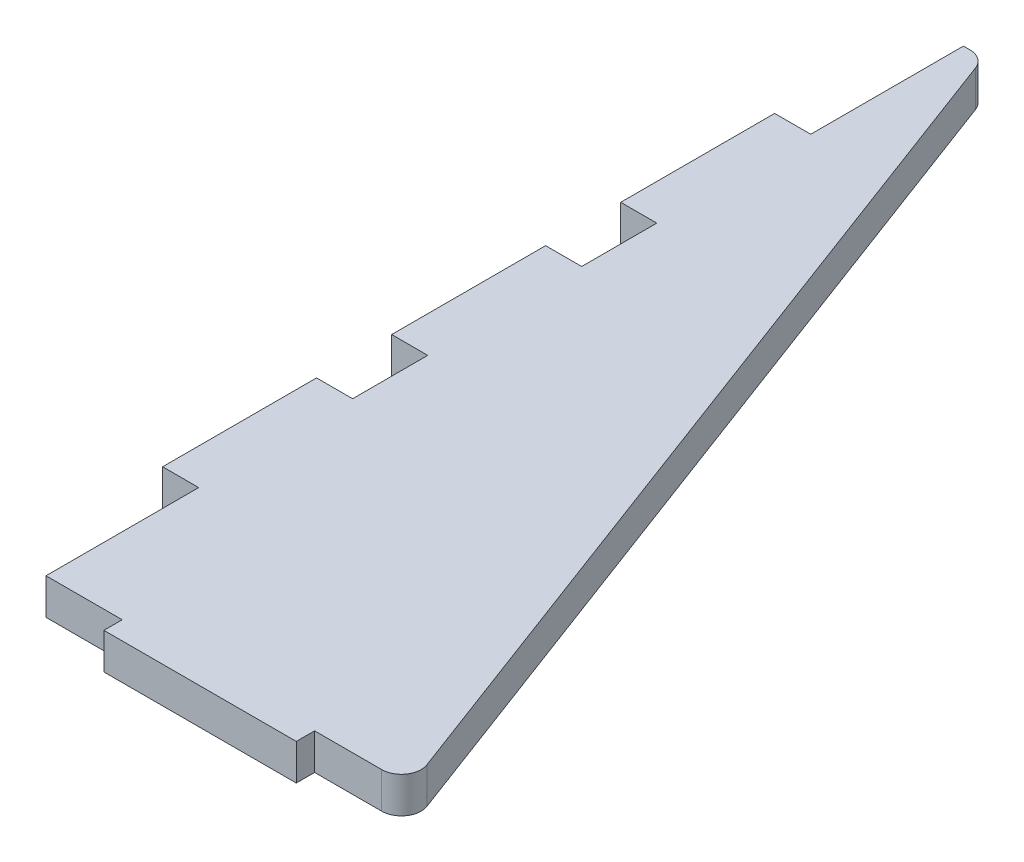
SolidWorks part; units mm, degrees
material "Balsa"
ref_plane "Front Plane" through (0, 0, 0) normal (0, 0, 1) x (1, 0, 0)
ref_plane "Top Plane" through (0, 0, 0) normal (0, 1, 0) x (1, 0, 0)
ref_plane "Right Plane" through (0, 0, 0) normal (1, 0, 0) x (0, 0, -1)
sketch "Sketch1" plane through (0, 0, 0) normal (0, 1, 0) x (1, 0, 0)
  line L0 (-3.175, 76.2) -> (-3.175, -76.2)
  line L1 (-3.175, -76.2) -> (57.15, -76.2)
  line L2 (57.15, -76.2) -> (0, 76.2)
  line L3 (0, 76.2) -> (-3.175, 76.2)
  point P2 (0, 0)
  point P5 (0, 0)
  point P7 (28.575, 0)
  dimension "D1" = 152.4
  dimension "D2" = 3.175
  dimension "D3" = 57.15
extrude "Boss-Extrude1" add sketch "Sketch1" along normal blind 6 contours L2 L3 L0 L1
sketch "Sketch2" plane through (0, 0, 0) normal (0, 1, 0) x (1, 0, 0)
  line L0 (-3.175, 76.2) -> (-3.175, -76.2) construction
  line L1 (-3.175, -12.7) -> (-9.175, -12.7)
  line L2 (-3.175, -12.7) -> (-3.175, 12.7)
  line L3 (-3.175, 12.7) -> (-9.175, 12.7)
  line L4 (-9.175, -12.7) -> (-9.175, 12.7)
  line L5 (-25.5719, 0) -> (49.4388, 0) construction
  line L6 (-3.175, 25.4) -> (-9.175, 25.4)
  line L7 (-3.175, 25.4) -> (-3.175, 50.8)
  line L8 (-3.175, 50.8) -> (-9.175, 50.8)
  line L9 (-9.175, 25.4) -> (-9.175, 50.8)
  line L10 (-3.175, -25.4) -> (-3.175, -50.8)
  line L11 (-3.175, -25.4) -> (-9.175, -25.4)
  line L12 (-9.175, -25.4) -> (-9.175, -50.8)
  line L13 (-3.175, -50.8) -> (-9.175, -50.8)
  line L14 (-3.175, -76.2) -> (57.15, -76.2) construction
  line L15 (9.4996, -76.2) -> (41.3004, -76.2)
  line L16 (9.4996, -76.2) -> (9.4996, -79.248)
  line L17 (9.4996, -79.248) -> (41.3004, -79.248)
  line L18 (41.3004, -76.2) -> (41.3004, -79.248)
  point P13 (-9.175, 0)
  point P14 (-9.175, 38.1)
  point P25 (25.4, -79.248)
  dimension "D1" = 6
  dimension "D2" = 25.4
  dimension "D3" = 38.1
  dimension "D4" = 25.4
  dimension "D5" = 31.8008
  dimension "D6" = 3.048
extrude "Boss-Extrude4" add sketch "Sketch2" along normal up to surface (6 mm away) up to face at (12.7, 6, 0)
fillet "Fillet1" radius 3.175 2 edges at (57.15, 3, 76.2) (0, 3, -76.2)
sketch "Sketch3" plane through (0, 6, 0) normal (0, 1, 0) x (1, 0, 0)
  line L40 (41.402, -76.3016) -> (52.5685, -76.3016)
  line L41 (55.6364, -71.8745) -> (0.8677, 74.1755)
  line L42 (-2.2003, 76.3016) -> (-3.2766, 76.3016)
  line L43 (-3.2766, 76.3016) -> (-3.2766, 50.9016)
  line L44 (-3.2766, 50.9016) -> (-9.2766, 50.9016)
  line L45 (-9.2766, 50.9016) -> (-9.2766, 25.2984)
  line L46 (-9.2766, 25.2984) -> (-3.2766, 25.2984)
  line L47 (-3.2766, 25.2984) -> (-3.2766, 12.8016)
  line L48 (-3.2766, 12.8016) -> (-9.2766, 12.8016)
  line L49 (-9.2766, 12.8016) -> (-9.2766, -12.8016)
  line L50 (-9.2766, -12.8016) -> (-3.2766, -12.8016)
  line L51 (-3.2766, -12.8016) -> (-3.2766, -25.2984)
  line L52 (-3.2766, -25.2984) -> (-9.2766, -25.2984)
  line L53 (-9.2766, -25.2984) -> (-9.2766, -50.9016)
  line L54 (-9.2766, -50.9016) -> (-3.2766, -50.9016)
  line L55 (-3.2766, -50.9016) -> (-3.2766, -76.3016)
  line L56 (-3.2766, -76.3016) -> (9.398, -76.3016)
  line L57 (9.398, -76.3016) -> (9.398, -79.3496)
  line L58 (9.398, -79.3496) -> (41.402, -79.3496)
  line L59 (41.402, -79.3496) -> (41.402, -76.3016)
  line L60 (41.402, -76.3016) -> (52.5685, -76.3016)
  line L61 (55.6364, -71.8745) -> (0.8677, 74.1755)
  line L62 (-2.2003, 76.3016) -> (-3.2766, 76.3016)
  line L63 (-3.2766, 76.3016) -> (-3.2766, 50.9016)
  line L64 (-3.2766, 50.9016) -> (-9.2766, 50.9016)
  line L65 (-9.2766, 50.9016) -> (-9.2766, 25.2984)
  line L66 (-9.2766, 25.2984) -> (-3.2766, 25.2984)
  line L67 (-3.2766, 25.2984) -> (-3.2766, 12.8016)
  line L68 (-3.2766, 12.8016) -> (-9.2766, 12.8016)
  line L69 (-9.2766, 12.8016) -> (-9.2766, -12.8016)
  line L70 (-9.2766, -12.8016) -> (-3.2766, -12.8016)
  line L71 (-3.2766, -12.8016) -> (-3.2766, -25.2984)
  line L72 (-3.2766, -25.2984) -> (-9.2766, -25.2984)
  line L73 (-9.2766, -25.2984) -> (-9.2766, -50.9016)
  line L74 (-9.2766, -50.9016) -> (-3.2766, -50.9016)
  line L75 (-3.2766, -50.9016) -> (-3.2766, -76.3016)
  line L76 (-3.2766, -76.3016) -> (9.398, -76.3016)
  line L77 (9.398, -76.3016) -> (9.398, -79.3496)
  line L78 (9.398, -79.3496) -> (41.402, -79.3496)
  line L79 (41.402, -79.3496) -> (41.402, -76.3016)
  arc A4 (52.5685, -76.3016) -> (55.6364, -71.8745) centre (52.5685, -73.025) ccw
  arc A5 (0.8677, 74.1755) -> (-2.2003, 76.3016) centre (-2.2003, 73.025) ccw
  arc A6 (52.5685, -76.3016) -> (55.6364, -71.8745) centre (52.5685, -73.025) ccw
  arc A7 (0.8677, 74.1755) -> (-2.2003, 76.3016) centre (-2.2003, 73.025) ccw
  dimension "D1" = 0.1016
extrude "KERF" add sketch "Sketch3" against normal up to surface (6 mm away) contours L60 A6 L61 A7 L62 L63 L64 L65 L66 L67 L68 L69 L70 L71 L72 L73 L74 L75 L76 L77 L78 L79 up to face at (5.8762, 0, 14.0445)
